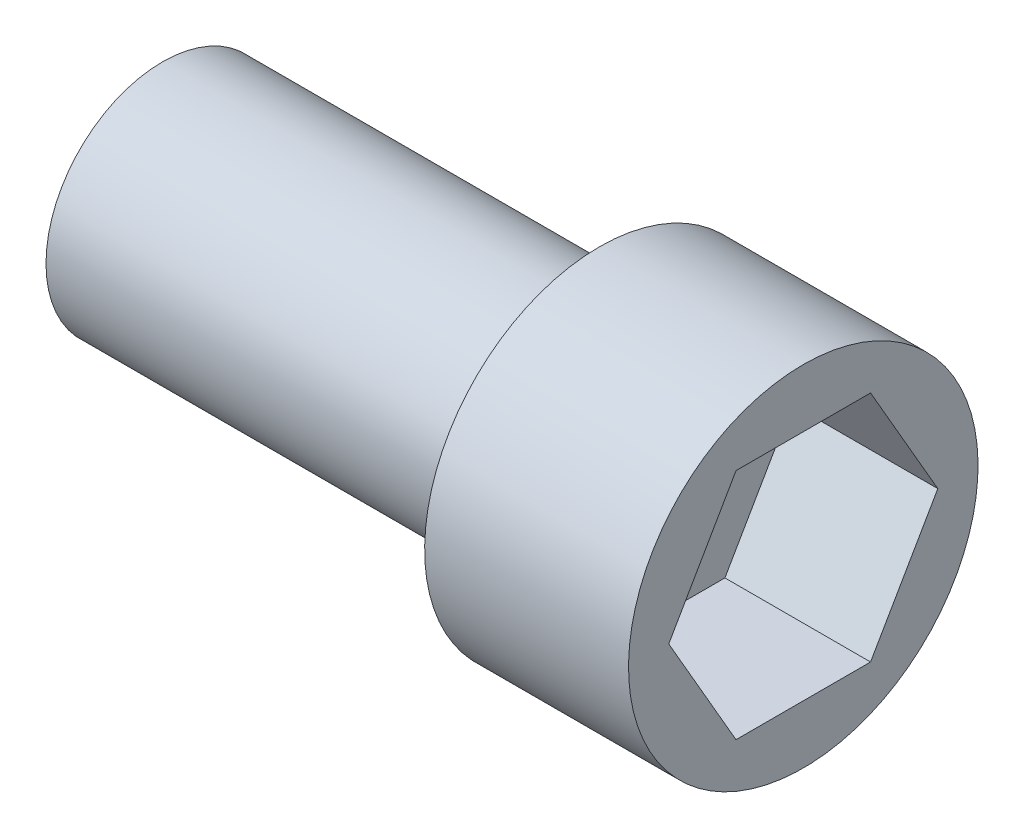
SolidWorks part; units mm, degrees
ref_plane "Front Plane" through (0, 0, 0) normal (0, 0, 1) x (1, 0, 0)
ref_plane "Top Plane" through (0, 0, 0) normal (0, 1, 0) x (1, 0, 0)
ref_plane "Right Plane" through (0, 0, 0) normal (1, 0, 0) x (0, 0, -1)
sketch "Sketch1" plane through (0, 0, 0) normal (0, 0, 1) x (1, 0, 0)
  line L0 (11, 0) -> (-11, 0)
  line L1 (-11, 0) -> (-11, 4)
  line L2 (-11, 4) -> (4, 4)
  line L3 (4, 4) -> (4, 6)
  line L4 (4, 6) -> (11, 6)
  line L5 (11, 6) -> (11, 0)
  dimension "D1" = 15
  dimension "D2" = 7
  dimension "D3" = 4
  dimension "D4" = 2
  dimension "D5" = 11
revolve "Revolve1" add sketch "Sketch1" angle 360 about L0
sketch "Sketch2" plane through (11, 0, 0) normal (1, 0, 0) x (0, 0, -1)
  line L1 (4.6188, 0) -> (2.3094, 4)
  line L2 (2.3094, 4) -> (-2.3094, 4)
  line L3 (-2.3094, 4) -> (-4.6188, 0)
  line L4 (-4.6188, 0) -> (-2.3094, -4)
  line L5 (-2.3094, -4) -> (2.3094, -4)
  line L6 (2.3094, -4) -> (4.6188, 0)
  circle A0 centre (0, 0) radius 4 construction
  point P1 (0, 0)
  dimension "D1" = 8
extrude "Cut-Extrude2" cut sketch "Sketch2" against normal blind 5
